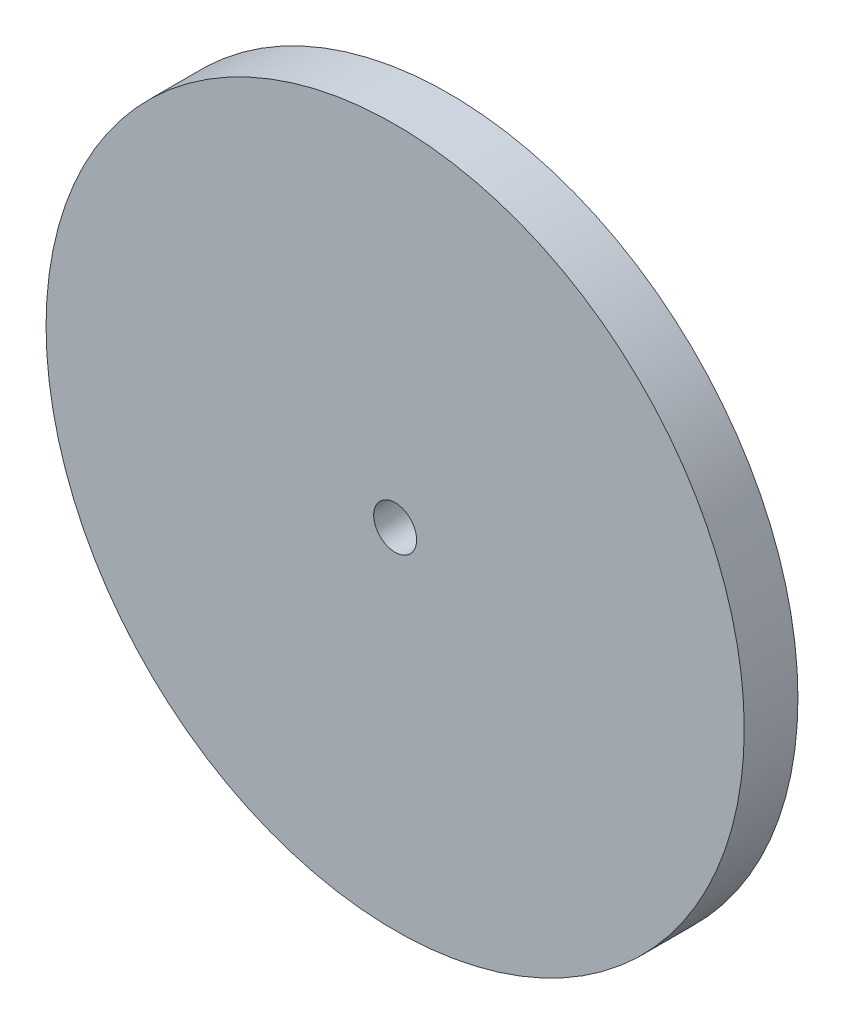
SolidWorks part; units mm, degrees
ref_plane "Front Plane" through (0, 0, 0) normal (0, 0, 1) x (1, 0, 0)
ref_plane "Top Plane" through (0, 0, 0) normal (0, 1, 0) x (1, 0, 0)
ref_plane "Right Plane" through (0, 0, 0) normal (1, 0, 0) x (0, 0, -1)
sketch "Sketch1" plane through (0, 0, 0) normal (0, 0, 1) x (1, 0, 0)
  circle A0 centre (0, 0) radius 0.4
  circle A1 centre (0, 0) radius 6.5
  dimension "D1" = 0.8
  dimension "D2" = 13
extrude "Boss-Extrude1" add sketch "Sketch1" along normal blind 1
